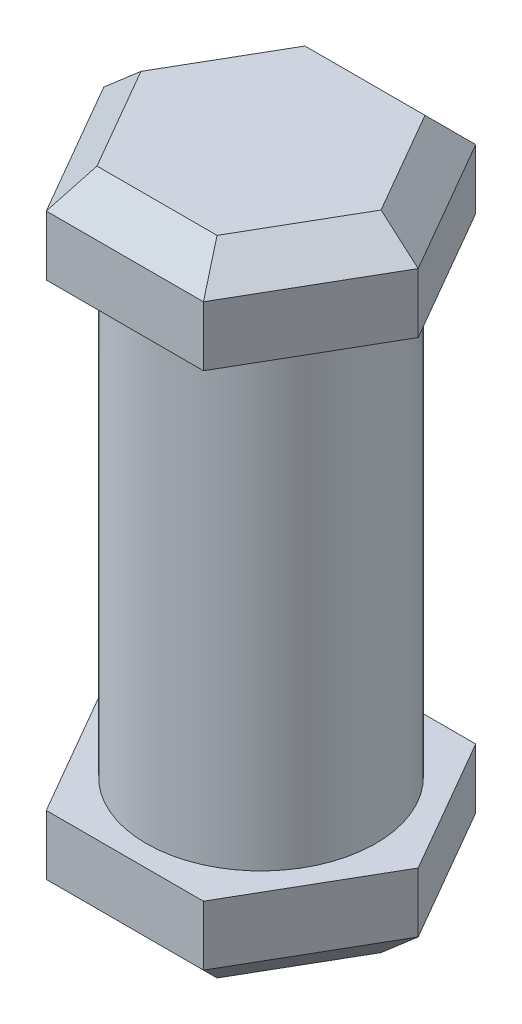
SolidWorks part; units mm, degrees
material "Zinc AC41A Alloy, As Cast"
ref_plane "Front Plane" through (0, 0, 0) normal (0, 0, 1) x (1, 0, 0)
ref_plane "Top Plane" through (0, 0, 0) normal (0, 1, 0) x (1, 0, 0)
ref_plane "Right Plane" through (0, 0, 0) normal (1, 0, 0) x (0, 0, -1)
sketch "Sketch1" plane through (0, 0, 0) normal (0, 1, 0) x (1, 0, 0)
  circle A0 centre (0, 0) radius 2.5
  dimension "D1" = 5
extrude "Boss-Extrude1" add sketch "Sketch1" along normal blind 10
sketch "Sketch2" plane through (0, 10, 0) normal (0, 1, 0) x (1, 0, 0)
  line L1 (3.4219, 0) -> (1.7109, 2.9634)
  line L2 (1.7109, 2.9634) -> (-1.7109, 2.9634)
  line L3 (-1.7109, 2.9634) -> (-3.4219, 0)
  line L4 (-3.4219, 0) -> (-1.7109, -2.9634)
  line L5 (-1.7109, -2.9634) -> (1.7109, -2.9634)
  line L6 (1.7109, -2.9634) -> (3.4219, 0)
  circle A0 centre (0, 0) radius 2.9634 construction
sketch "Sketch3" plane through (0, 0, 0) normal (0, -1, 0) x (1, 0, 0)
  line L1 (3.4219, 0) -> (1.7109, 2.9634)
  line L2 (1.7109, 2.9634) -> (-1.7109, 2.9634)
  line L3 (-1.7109, 2.9634) -> (-3.4219, 0)
  line L4 (-3.4219, 0) -> (-1.7109, -2.9634)
  line L5 (-1.7109, -2.9634) -> (1.7109, -2.9634)
  line L6 (1.7109, -2.9634) -> (3.4219, 0)
  circle A0 centre (0, 0) radius 2.9634 construction
extrude "Boss-Extrude2" add sketch "Sketch3" along normal blind 2
extrude "Boss-Extrude3" add sketch "Sketch2" along normal blind 2 contours L3 L4 L5 L6 L1 L2
chamfer "Chamfer1" distance 0.7 angle 45 12 edges at (0, -2, -2.9634) (-2.5664, -2, -1.4817) (-2.5664, -2, 1.4817) (0, -2, 2.9634) (2.5664, -2, 1.4817) (2.5664, -2, -1.4817) (2.5664, 12, -1.4817) (2.5664, 12, 1.4817) (0, 12, 2.9634) (-2.5664, 12, 1.4817) (-2.5664, 12, -1.4817) (0, 12, -2.9634)
